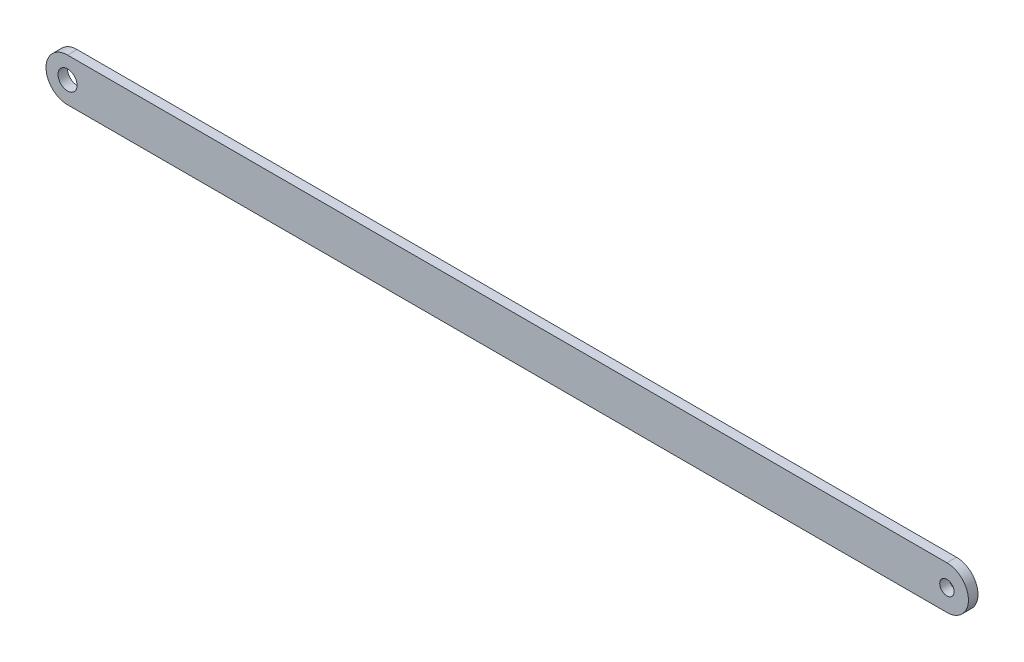
SolidWorks part; units mm, degrees
ref_plane "Front Plane" through (0, 0, 0) normal (0, 0, 1) x (1, 0, 0)
ref_plane "Top Plane" through (0, 0, 0) normal (0, 1, 0) x (1, 0, 0)
ref_plane "Right Plane" through (0, 0, 0) normal (1, 0, 0) x (0, 0, -1)
sketch "Sketch1" plane through (0, 0, 0) normal (0, 0, 1) x (1, 0, 0)
  line L0 (-16.2948, 9) -> (351.2352, 9)
  line L1 (-16.2948, 0) -> (351.2352, 0) construction
  line L2 (-16.2948, -9) -> (351.2352, -9)
  circle A0 centre (-16.2948, 0) radius 4
  circle A1 centre (351.2352, 0) radius 3
  arc A2 (351.2352, 9) -> (351.2352, -9) centre (351.2352, 0) cw
  arc A3 (-16.2948, 9) -> (-16.2948, -9) centre (-16.2948, 0) ccw
  dimension "D1" = 8
  dimension "D2" = 6
  dimension "D3" = 367.53
  dimension "D4" = 9
extrude "Boss-Extrude1" add sketch "Sketch1" along normal blind 4
